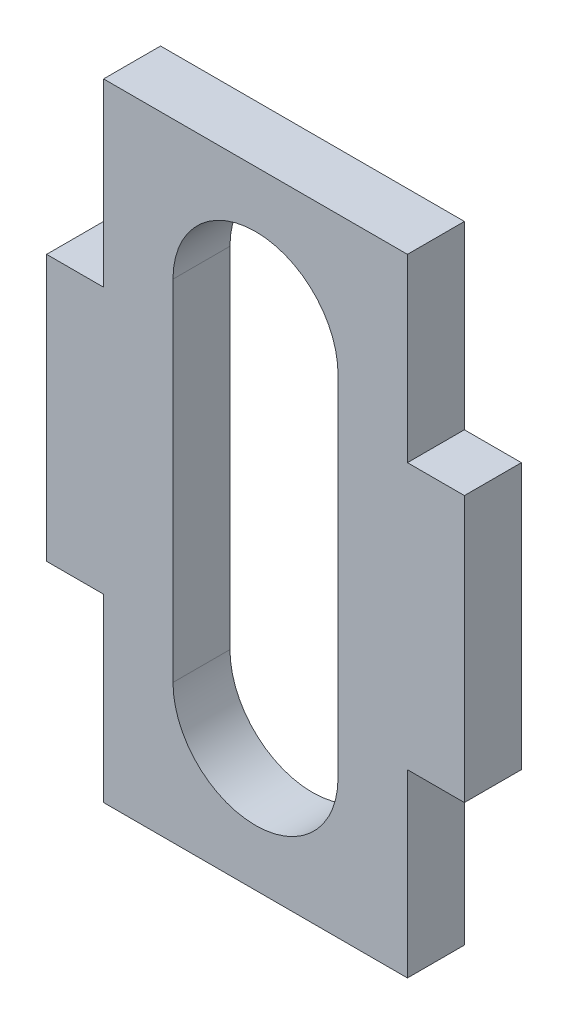
SolidWorks part; units mm, degrees
ref_plane "Front Plane" through (0, 0, 0) normal (0, 0, 1) x (1, 0, 0)
ref_plane "Top Plane" through (0, 0, 0) normal (0, 1, 0) x (1, 0, 0)
ref_plane "Right Plane" through (0, 0, 0) normal (1, 0, 0) x (0, 0, -1)
sketch "Sketch1" plane through (0, 0, 0) normal (0, 0, 1) x (1, 0, 0)
  line L1 (-8, -16.5) -> (8, -16.5)
  line L2 (-8, -16.5) -> (-8, 16.5)
  line L3 (-8, 16.5) -> (8, 16.5)
  line L4 (8, -16.5) -> (8, 16.5)
  line L5 (-8, -16.5) -> (8, 16.5) construction
  line L6 (-8, 16.5) -> (8, -16.5) construction
  point P0 (0, 0)
  dimension "D1" = 33
  dimension "D2" = 16
extrude "Boss-Extrude1" add sketch "Sketch1" along normal blind 3
sketch "Sketch2" plane through (0, 0, 3) normal (0, 0, 1) x (1, 0, 0)
  line L1 (-11, -7) -> (11, -7)
  line L2 (-11, -7) -> (-11, 7)
  line L3 (-11, 7) -> (11, 7)
  line L4 (11, -7) -> (11, 7)
  line L5 (-11, -7) -> (11, 7) construction
  line L6 (-11, 7) -> (11, -7) construction
  point P0 (0, 0)
  dimension "D1" = 14
  dimension "D2" = 22
extrude "Boss-Extrude2" add sketch "Sketch2" against normal blind 3
sketch "Sketch3" plane through (0, 0, 3) normal (0, 0, 1) x (1, 0, 0)
  line L0 (0, 9.1961) -> (0, -9.1961) construction
  line L1 (4.3455, 9.1961) -> (4.3455, -9.1961)
  line L2 (-4.3455, 9.1961) -> (-4.3455, -9.1961)
  arc A0 (4.3455, 9.1961) -> (-4.3455, 9.1961) centre (0, 9.1961) ccw
  arc A1 (-4.3455, -9.1961) -> (4.3455, -9.1961) centre (0, -9.1961) ccw
  point P3 (0, 0)
  point P8 (0, 0)
  point P9 (0, 5.4548)
extrude "Cut-Extrude1" cut sketch "Sketch3" against normal blind 10
